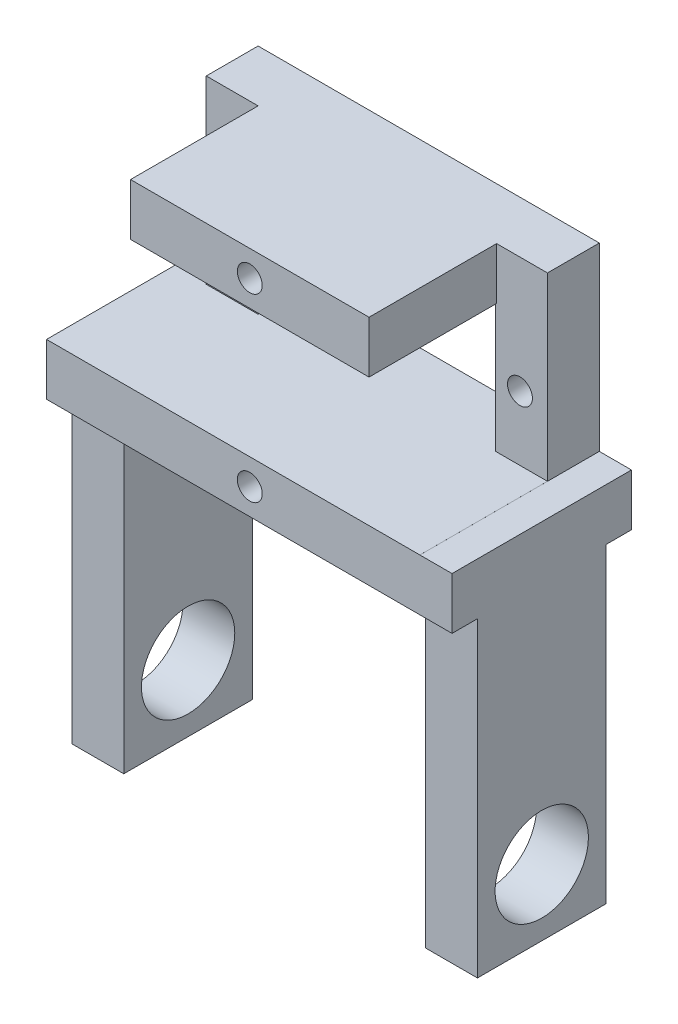
SolidWorks part; units mm, degrees
ref_plane "Front Plane" through (0, 0, 0) normal (0, 0, 1) x (1, 0, 0)
ref_plane "Top Plane" through (0, 0, 0) normal (0, 1, 0) x (1, 0, 0)
ref_plane "Right Plane" through (0, 0, 0) normal (1, 0, 0) x (0, 0, -1)
sketch "Sketch1" plane through (0, 0, 0) normal (0, 0, 1) x (1, 0, 0)
  line L1 (-16.45, 11.2) -> (16.45, 11.2)
  line L2 (-16.45, 11.2) -> (-16.45, -11.2)
  line L3 (-16.45, -11.2) -> (16.45, -11.2)
  line L4 (16.45, 11.2) -> (16.45, -11.2)
  line L5 (-16.45, 11.2) -> (16.45, -11.2) construction
  line L6 (-16.45, -11.2) -> (16.45, 11.2) construction
  point P0 (0, 0)
  dimension "D1" = 32.9
  dimension "22.4" = 22.4
extrude "Boss-Extrude1" add sketch "Sketch1" along normal blind 5
sketch "Sketch2" plane through (0, 0, 5) normal (0, 0, 1) x (1, 0, 0)
  line L0 (0, 0) -> (13.8, 0) construction
  line L1 (-11.45, 6.2) -> (11.45, 6.2)
  line L2 (-11.45, 6.2) -> (-11.45, -6.2)
  line L3 (-11.45, -6.2) -> (11.45, -6.2)
  line L4 (11.45, 6.2) -> (11.45, -6.2)
  line L5 (-11.45, 6.2) -> (11.45, -6.2) construction
  line L6 (-11.45, -6.2) -> (11.45, 6.2) construction
  line L7 (0, 0) -> (-13.8, 0) construction
  circle A0 centre (13.8, 0) radius 1.2
  circle A1 centre (-13.8, 0) radius 1.2
  point P0 (0, 0)
  dimension "D3" = 13.8
  dimension "D1" = 22.9
  dimension "D2" = 13.8
  dimension "12.4" = 12.4
extrude "Cut-Extrude2" cut sketch "Sketch2" against normal blind 5
sketch "Sketch3" plane through (0, 0, 5) normal (0, 0, 1) x (1, 0, 0)
  line L0 (16.45, 11.2) -> (-16.45, 11.2) construction
  line L1 (-11.45, 6.2) -> (11.5469, 6.2)
  line L2 (-11.45, 6.2) -> (-11.45, 11.2)
  line L3 (-11.45, 11.2) -> (11.5469, 11.2)
  line L4 (11.5469, 6.2) -> (11.5469, 11.2)
  line L5 (-16.45, -11.2) -> (16.45, -11.2) construction
  line L6 (-11.45, -6.2) -> (11.5469, -6.2)
  line L7 (-11.45, -6.2) -> (-11.45, -11.2)
  line L8 (-11.45, -11.2) -> (11.5469, -11.2)
  line L9 (11.5469, -6.2) -> (11.5469, -11.2)
extrude "Boss-Extrude2" add sketch "Sketch3" along normal blind 12.3
sketch "Sketch4" plane through (0, 0, 17.3) normal (0, 0, 1) x (1, 0, 0)
  line L0 (0.0484, 11.2) -> (0.0484, 6.2) construction
  line L1 (11.5469, 11.2) -> (-11.45, 11.2) construction
  line L2 (-11.45, 6.2) -> (11.5469, 6.2) construction
  line L3 (0.0484, -6.2) -> (0.0484, -11.2) construction
  line L4 (11.5469, -6.2) -> (-11.45, -6.2) construction
  line L5 (-11.45, -11.2) -> (11.5469, -11.2) construction
  circle A0 centre (0.0484, 8.7) radius 1.2
  circle A1 centre (0.0484, -8.7) radius 1.2
extrude "Cut-Extrude3" cut sketch "Sketch4" against normal blind 5
sketch "Sketch6" plane through (0, 0, 5) normal (0, 0, 1) x (1, 0, 0)
  line L0 (-11.45, 6.2) -> (-11.45, -6.2) construction
  line L1 (-16.45, -11.2) -> (-11.45, -11.2)
  line L2 (-16.45, -11.2) -> (-16.45, -6.2)
  line L3 (-16.45, -6.2) -> (-11.45, -6.2)
  line L4 (-11.45, -11.2) -> (-11.45, -6.2)
  line L5 (-11.45, -6.2) -> (-11.45, -11.2) construction
  line L6 (16.45, -11.2) -> (16.45, 11.2) construction
  line L7 (11.5469, -11.2) -> (16.45, -11.2)
  line L8 (11.5469, -11.2) -> (11.5469, -6.2)
  line L9 (11.5469, -6.2) -> (16.45, -6.2)
  line L10 (16.45, -11.2) -> (16.45, -6.2)
extrude "Boss-Extrude3" add sketch "Sketch6" along normal blind 12.3
sketch "Sketch8" plane through (16.45, 0, 0) normal (1, 0, 0) x (0, 0, -1)
  line L0 (0, -11.2) -> (0, 11.2) construction
  line L1 (-17.3, -11.2) -> (0, -11.2)
  line L2 (-17.3, -11.2) -> (-17.3, -6.2018)
  line L3 (-17.3, -6.2018) -> (0, -6.2018)
  line L4 (0, -11.2) -> (0, -6.2018)
extrude "Boss-Extrude4" add sketch "Sketch8" along normal blind 3.1
sketch "Sketch9" plane through (-16.45, 0, 0) normal (-1, 0, 0) x (0, 0, 1)
  line L1 (0, -11.2) -> (17.3, -11.2)
  line L2 (0, -11.2) -> (0, -6.2)
  line L3 (0, -6.2) -> (17.3, -6.2)
  line L4 (17.3, -11.2) -> (17.3, -6.2)
extrude "Boss-Extrude5" add sketch "Sketch9" along normal blind 3.1
sketch "Sketch10" plane through (0, -11.2, 0) normal (0, -1, 0) x (1, 0, 0)
  line L0 (19.55, 8.65) -> (17.05, 8.65) construction
  line L1 (19.55, 17.3) -> (19.55, 0) construction
  line L2 (-19.55, 8.65) -> (-17.05, 8.65) construction
  line L3 (-19.55, 0) -> (-19.55, 17.3) construction
  line L5 (14.55, 14.85) -> (19.55, 14.85)
  line L6 (14.55, 14.85) -> (14.55, 2.45)
  line L7 (14.55, 2.45) -> (19.55, 2.45)
  line L8 (19.55, 14.85) -> (19.55, 2.45)
  line L9 (14.55, 14.85) -> (19.55, 2.45) construction
  line L10 (14.55, 2.45) -> (19.55, 14.85) construction
  line L11 (-14.55, 14.85) -> (-19.55, 14.85)
  line L12 (-14.55, 14.85) -> (-14.55, 2.45)
  line L13 (-14.55, 2.45) -> (-19.55, 2.45)
  line L14 (-19.55, 14.85) -> (-19.55, 2.45)
  line L15 (-14.55, 14.85) -> (-19.55, 2.45) construction
  line L16 (-14.55, 2.45) -> (-19.55, 14.85) construction
  dimension "D1" = 12.4
sketch "Sketch18" plane through (0, -11.2, 0) normal (0, -1, 0) x (1, 0, 0)
  line L0 (-19.55, 8.65) -> (-17.05, 8.65) construction
  line L1 (-19.55, 0) -> (-19.55, 17.3) construction
  line L2 (19.55, 8.65) -> (17.05, 8.65) construction
  line L4 (19.55, 17.3) -> (19.55, 0) construction
  line L5 (-14.55, 2.45) -> (-19.55, 2.45)
  line L6 (-14.55, 2.45) -> (-14.55, 14.85)
  line L7 (-14.55, 14.85) -> (-19.55, 14.85)
  line L8 (-19.55, 2.45) -> (-19.55, 14.85)
  line L9 (-14.55, 2.45) -> (-19.55, 14.85) construction
  line L10 (-14.55, 14.85) -> (-19.55, 2.45) construction
  line L12 (14.55, 2.45) -> (19.55, 2.45)
  line L13 (14.55, 2.45) -> (14.55, 14.85)
  line L14 (14.55, 14.85) -> (19.55, 14.85)
  line L15 (19.55, 2.45) -> (19.55, 14.85)
  line L16 (14.55, 2.45) -> (19.55, 14.85) construction
  line L17 (14.55, 14.85) -> (19.55, 2.45) construction
  dimension "D1" = 12.4
extrude "Boss-Extrude7" add sketch "Sketch18" along normal blind 30
sketch "Sketch19" plane through (-19.55, 0, 0) normal (-1, 0, 0) x (0, 0, 1)
  line L0 (8.65, -41.2) -> (8.65, -34.8) construction
  line L1 (14.85, -41.2) -> (2.45, -41.2) construction
  circle A0 centre (8.65, -34.8) radius 4.5
extrude "Cut-Extrude6" cut sketch "Sketch19" against normal blind 30
sketch "Sketch20" plane through (19.55, 0, 0) normal (1, 0, 0) x (0, 0, -1)
  line L0 (-8.65, -41.2) -> (-8.65, -34.8) construction
  line L1 (-2.45, -41.2) -> (-14.85, -41.2) construction
  circle A0 centre (-8.65, -34.8) radius 4.5
extrude "Cut-Extrude7" cut sketch "Sketch20" against normal blind 30
extrude "Boss-Extrude6" add sketch "Sketch10" along normal blind 30
sketch "Sketch12" plane through (-19.55, 0, 0) normal (-1, 0, 0) x (0, 0, 1)
sketch "Sketch21" plane through (19.55, 0, 0) normal (1, 0, 0) x (0, 0, -1)
  line L0 (-8.65, -41.2) -> (-8.65, -34.8) construction
  line L1 (-2.45, -41.2) -> (-14.85, -41.2) construction
  circle A0 centre (-8.65, -34.8) radius 4.5
extrude "Cut-Extrude8" cut sketch "Sketch21" against normal blind 10
sketch "Sketch22" plane through (-14.55, 0, 0) normal (1, 0, 0) x (0, 0, -1)
  line L0 (-8.65, -41.2) -> (-8.65, -34.8) construction
  line L1 (-2.45, -41.2) -> (-14.85, -41.2) construction
  circle A0 centre (-8.65, -34.8) radius 4.5
extrude "Cut-Extrude9" cut sketch "Sketch22" against normal blind 10
